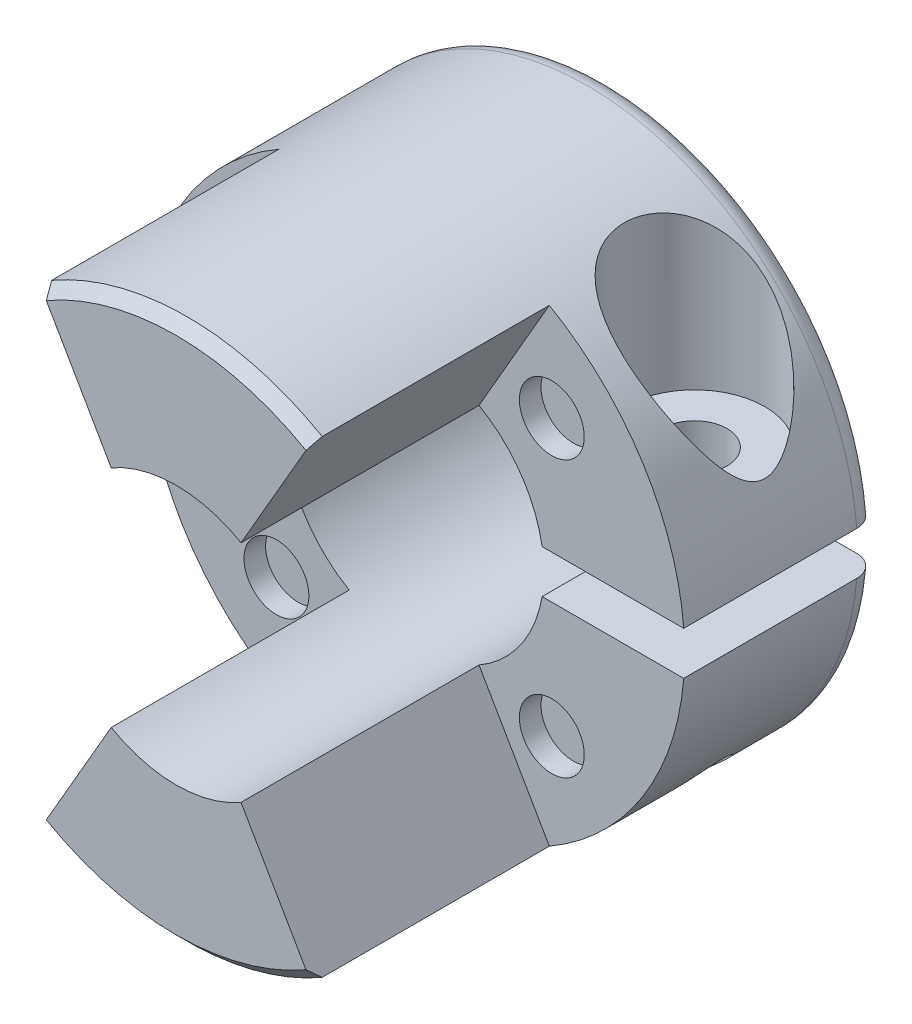
SolidWorks part; units mm, degrees
material "Liga 6061"
ref_plane "Plano frontal" through (0, 0, 0) normal (0, 0, 1) x (1, 0, 0)
ref_plane "Plano superior" through (0, 0, 0) normal (0, 1, 0) x (1, 0, 0)
ref_plane "Plano direito" through (0, 0, 0) normal (1, 0, 0) x (0, 0, -1)
sketch "Esboço1" plane through (0, 0, 0) normal (0, 0, 1) x (1, 0, 0)
  circle A0 centre (0, 0) radius 12.5
  dimension "D1" = 25
extrude "Ressalto-extrusão1" add sketch "Esboço1" along normal blind 20
sketch "Esboço2" plane through (0, 0, 20) normal (0, 0, 1) x (1, 0, 0)
  line L0 (0, 0) -> (0, 12.5) construction
  line L1 (0, 0) -> (6.25, 10.8253)
  line L2 (6.25, -10.8253) -> (0, 0)
  circle A0 centre (0, 0) radius 12.5 construction
  arc A2 (6.25, 10.8253) -> (6.25, -10.8253) centre (0, 0) cw
  dimension "D1" = 120
  dimension "D2" = 30
extrude "Corte-extrusão3" cut sketch "Esboço2" against normal blind 11
sketch "Esboço3" plane through (0, 0, 0) normal (0, 0, -1) x (-1, 0, 0)
  circle A0 centre (0, 0) radius 6
  dimension "D1" = 12
extrude "Corte-extrusão4" cut sketch "Esboço3" against normal through all
mirror "Espelhar1" about plane through (0, 0, 0) normal (1, 0, 0) of "Corte-extrusão3"
sketch "Esboço6" plane through (0, 0, 9) normal (0, 0, 1) x (1, 0, 0)
  line L1 (1, 1) -> (13, 1)
  line L2 (1, 1) -> (1, -1)
  line L3 (1, -1) -> (13, -1)
  line L4 (13, 1) -> (13, -1)
  line L5 (1, 1) -> (13, -1) construction
  line L6 (1, -1) -> (13, 1) construction
  point P0 (7, 0)
  dimension "D1" = 2
  dimension "D2" = 12
  dimension "D3" = 7
extrude "Corte-extrusão5" cut sketch "Esboço6" against normal through all
sketch "Esboço7" plane through (0, 1, 0) normal (0, -1, 0) x (1, 0, 0)
  line L0 (12.4599, 9) -> (12.4599, 0) construction
  circle A0 centre (8.4599, 4.5) radius 3.25
  point P4 (12.4599, 4.5)
  dimension "D1" = 6.5
  dimension "D2" = 4
extrude "Corte-extrusão6" cut sketch "Esboço7" against normal through all from offset 3 offset against normal yes
hole_wizard "Furo roscado de M3x0.51" positions "Esboço9" profile "Esboço8" tap size "M3x0.5" standard "Ansi Metric" end condition through all
sketch "Esboço9" plane through (0, 4, 0) normal (0, 1, 0) x (1, 0, 0)
  point P0 (8.4599, -4.5)
sketch "Esboço8" plane through (8.4599, 4, 4.5) normal (1, 0, 0) x (0, 0, 1)
  line L0 (0, 0) -> (0, 16.5)
  line L1 (0, 16.5) -> (1.25, 16.5)
  line L2 (1.25, 16.5) -> (1.25, 0)
  line L5 (1.25, 0) -> (0, 0)
  line L11 (0, -6.35) -> (0, 107.95) construction
  dimension "Thru Tap Drill Dia." = 2.5
  dimension "Thru Tap Drill Depth" = 16.5
cosmetic thread "Hole Thread2" parameters "D2"=3
fillet "Filete1" radius 1 1 edges at (-12.5, 0, 0)
sketch "Esboço10" plane through (0, 0, 9) normal (0, 0, 1) x (1, 0, 0)
  line L0 (0, 0) -> (0, -3.9553) construction
  line L1 (6.364, -6.364) -> (0, 0) construction
  circle A0 centre (6.364, -6.364) radius 1.5
  dimension "D1" = 3
  dimension "D2" = 9
  dimension "D3" = 45
extrude "Corte-extrusão7" cut sketch "Esboço10" against normal blind 1
chamfer "Chanfro1" distance 0.5 angle 45 2 edges at (0, 12.5, 20) (0, -12.5, 20)
sketch "Esboço11" plane through (0, 4, 0) normal (0, 1, 0) x (1, 0, 0)
  circle A0 centre (8.4599, -4.5) radius 1.5
  dimension "D1" = 3
extrude "Corte-extrusão8" cut sketch "Esboço11" against normal up to next
sketch "Esboço12" plane through (0, 0, 20) normal (0, 0, 1) x (1, 0, 0)
  circle A0 centre (0, 0) radius 6
  dimension "D1" = 12
pattern_circular "PadrãoCircular1" count 4 over 360 about axis through (0, 0, 0) along (0, 0, 1) of "Corte-extrusão7"
chamfer "Chanfro2" distance 0.5 angle 45 1 edges at (-6, 0, 0)
